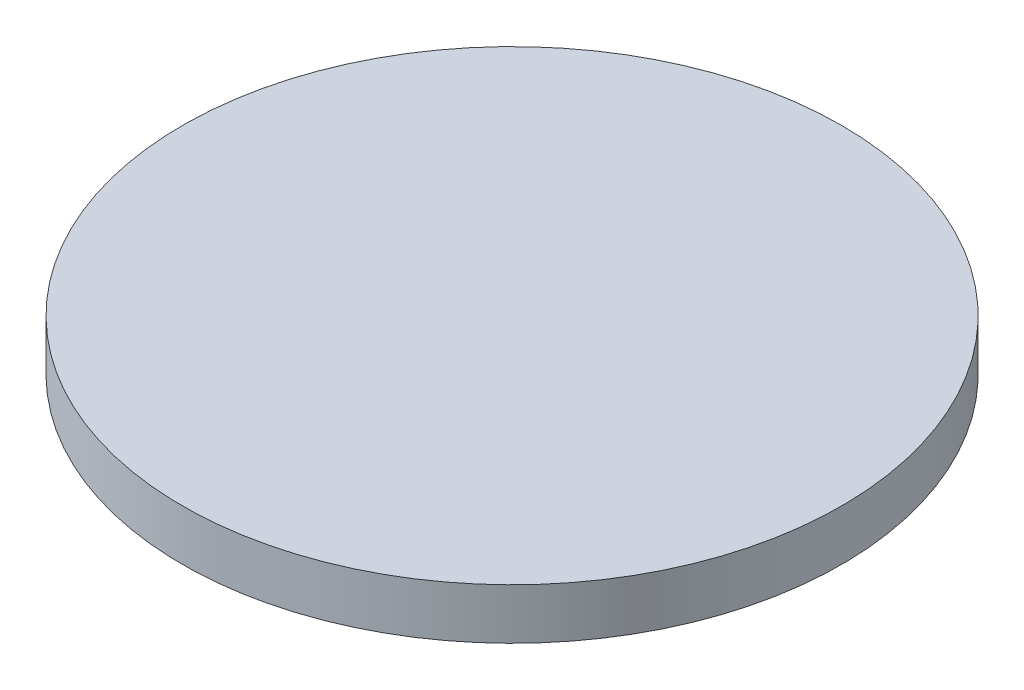
SolidWorks part; units mm, degrees
ref_plane "Front Plane" through (0, 0, 0) normal (0, 0, 1) x (1, 0, 0)
ref_plane "Top Plane" through (0, 0, 0) normal (0, 1, 0) x (1, 0, 0)
ref_plane "Right Plane" through (0, 0, 0) normal (1, 0, 0) x (0, 0, -1)
sketch "Sketch1" plane through (0, 0, 0) normal (0, 0, 1) x (1, 0, 0)
  line L0 (0, 0) -> (0, 15)
  line L1 (0, 15) -> (32.5, 15)
  line L2 (32.5, 15) -> (32.5, 10)
  line L3 (32.5, 10) -> (12.5, 0)
  line L4 (12.5, 0) -> (0, 0)
  dimension "D1" = 32.5
  dimension "D2" = 12.5
  dimension "D3" = 15
  dimension "D4" = 5
revolve "Revolve1" add sketch "Sketch1" angle 360 about L0
